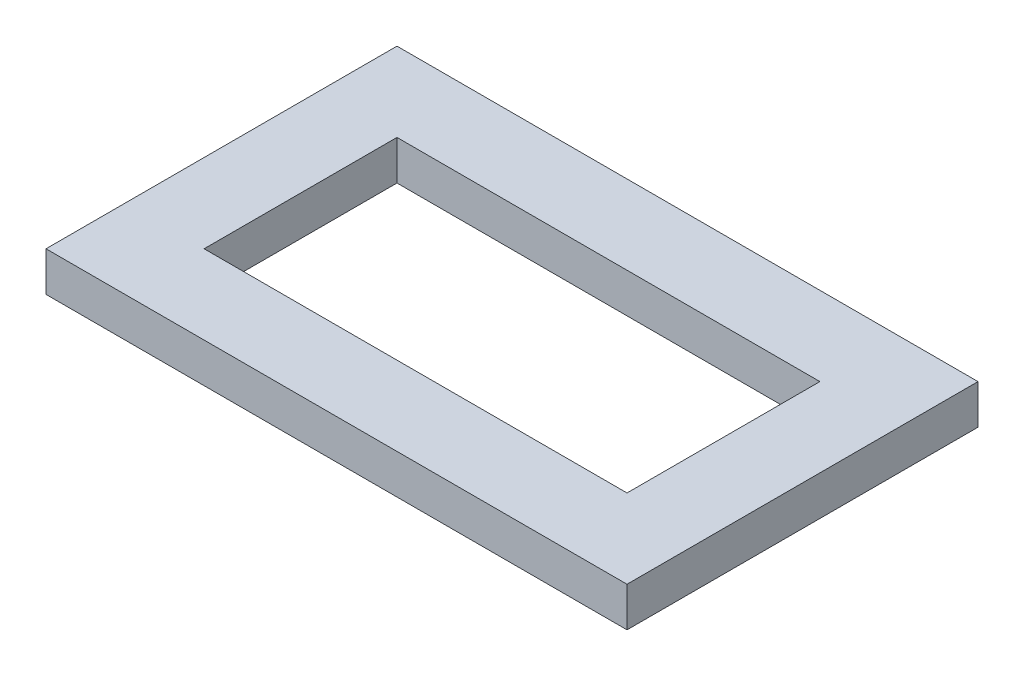
SolidWorks part; units mm, degrees
ref_plane "Front Plane" through (0, 0, 0) normal (0, 0, 1) x (1, 0, 0)
ref_plane "Top Plane" through (0, 0, 0) normal (0, 1, 0) x (1, 0, 0)
ref_plane "Right Plane" through (0, 0, 0) normal (1, 0, 0) x (0, 0, -1)
sketch "Sketch1" plane through (0, 0, 0) normal (0, 1, 0) x (1, 0, 0)
  line L0 (31.75, -5) -> (31.75, 17.2)
  line L1 (0, 0) -> (26.75, 0)
  line L2 (0, 0) -> (0, 12.2)
  line L3 (0, 12.2) -> (26.75, 12.2)
  line L4 (26.75, 0) -> (26.75, 12.2)
  line L5 (-5, 17.2) -> (31.75, 17.2)
  line L6 (-5, -5) -> (-5, 17.2)
  line L7 (-5, -5) -> (31.75, -5)
  dimension "D1" = 12.2
  dimension "D2" = 26.75
  dimension "D3" = 5
extrude "Boss-Extrude1" add sketch "Sketch1" along normal blind 2.5 contours L0 L5 L6 L7 | L2 L1 L4 L3
